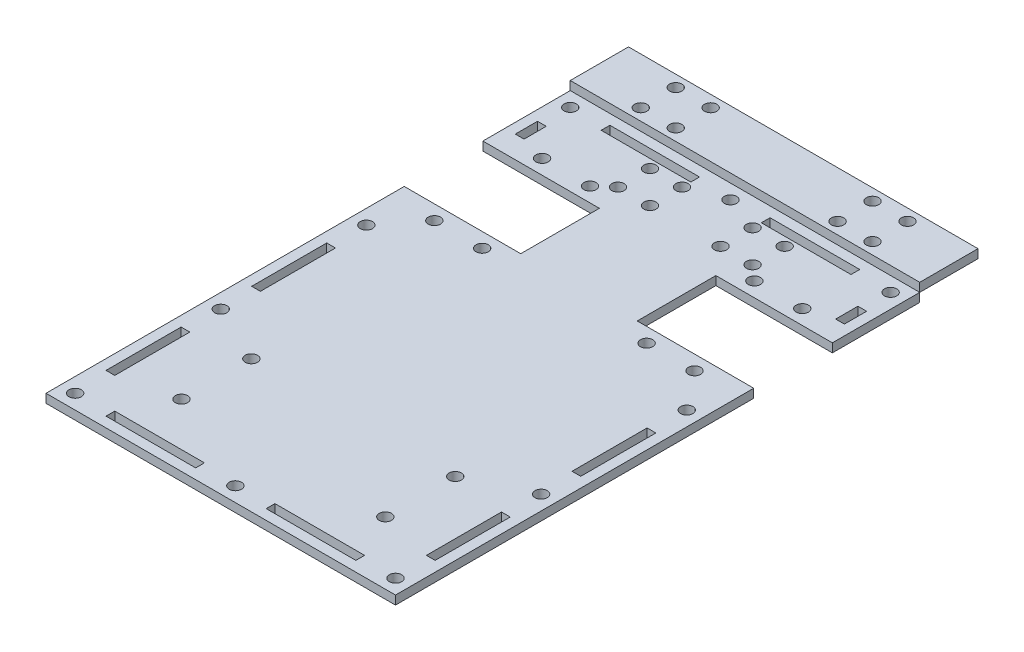
SolidWorks part; units mm, degrees
ref_plane "Front Plane" through (0, 0, 0) normal (0, 0, 1) x (1, 0, 0)
ref_plane "Top Plane" through (0, 0, 0) normal (0, 1, 0) x (1, 0, 0)
ref_plane "Right Plane" through (0, 0, 0) normal (1, 0, 0) x (0, 0, -1)
sketch "Sketch1" plane through (0, 0, 0) normal (0, 1, 0) x (1, 0, 0)
  line L0 (0, 0) -> (120, 0)
  line L1 (0, 0) -> (0, 110)
  line L2 (0, 110) -> (40, 110)
  line L3 (40, 110) -> (40, 150)
  line L4 (40, 150) -> (0, 150)
  line L5 (0, 150) -> (0, 180)
  line L6 (0, 180) -> (120, 180)
  line L7 (120, 180) -> (120, 150)
  line L8 (120, 150) -> (80, 150)
  line L11 (120, 110) -> (120, 0)
  line L12 (80, 150) -> (80, 110)
  line L13 (80, 110) -> (120, 110)
extrude "Boss-Extrude1" add sketch "Sketch1" along normal blind 3 contours L13 L11 L0 L1 L2 L3 L4 L5 L6 L7 L8 L12
sketch "Sketch2" plane through (0, 3, 0) normal (0, 1, 0) x (1, 0, 0)
  line L0 (5, 180) -> (5, 175)
  line L1 (0, 180) -> (120, 180) construction
  line L2 (5, 175) -> (0, 175)
  line L3 (0, 150) -> (0, 180) construction
  line L4 (60, 180) -> (60, 175)
  line L5 (115, 180) -> (115, 175)
  line L6 (115, 175) -> (120, 175)
  line L7 (5, 0) -> (5, 5)
  line L8 (0, 0) -> (120, 0) construction
  line L9 (5, 5) -> (0, 5)
  line L10 (0, 0) -> (0, 110) construction
  line L11 (60, 0) -> (60, 5)
  line L12 (115, 0) -> (115, 5)
  line L13 (115, 5) -> (120, 5)
  line L14 (5, 110) -> (5, 105)
  line L15 (0, 110) -> (40, 110) construction
  line L16 (5, 105) -> (0, 105)
  line L17 (115, 110) -> (115, 105)
  line L18 (115, 105) -> (120, 105)
  line L19 (115, 5) -> (115, 105)
  line L20 (5, 105) -> (5, 5)
  line L21 (115, 5) -> (106.5, 5)
  line L22 (5, 5) -> (13.5, 5)
  line L23 (60, 5) -> (60, 10)
  line L24 (25, 57) -> (25, 45.5)
  line L25 (13.5, 10) -> (106.5, 10)
  line L26 (13.5, 10) -> (13.5, 57)
  line L27 (13.5, 57) -> (106.5, 57)
  line L28 (106.5, 10) -> (106.5, 57)
  line L29 (25, 45.5) -> (13.5, 45.5)
  line L32 (95, 57) -> (95, 45.5)
  line L33 (95, 45.5) -> (106.5, 45.5)
  line L34 (95, 21.5) -> (106.5, 21.5)
  line L35 (95, 10) -> (95, 21.5)
  line L36 (25, 10) -> (25, 21.5)
  line L37 (25, 21.5) -> (13.5, 21.5)
hole_wizard "Hole for M3 300® SC Nuts (SP)1" positions "Sketch3" profile "Sketch4" hole size "M3x0.5" standard "PEM® Metric" end condition through all
sketch "Sketch3" plane through (0, 3, 0) normal (0, 1, 0) x (1, 0, 0)
  point P0 (5, 175)
  point P3 (60, 175)
  point P6 (115, 175)
  point P9 (115, 5)
  point P12 (60, 5)
  point P15 (5, 5)
sketch "Sketch4" plane through (5, 3, -175) normal (1, 0, 0) x (0, 0, 1)
  line L0 (0, 0) -> (0, 3)
  line L1 (0, 3) -> (2.11, 3)
  line L2 (2.11, 3) -> (2.11, 0)
  line L5 (2.11, 0) -> (0, 0)
  line L11 (0, -6.35) -> (0, 107.95) construction
  dimension "Thru Hole Dia." = 4.22
  dimension "Thru Hole Depth" = 3
hole_wizard "Hole for M3 300® SC Nuts (SP)2" positions "Sketch5" profile "Sketch6" hole size "M3x0.5" standard "PEM® Metric" end condition through all
sketch "Sketch5" plane through (0, 3, 0) normal (0, 1, 0) x (1, 0, 0)
  point P0 (5, 105)
  point P3 (115, 105)
sketch "Sketch6" plane through (5, 3, -105) normal (1, 0, 0) x (0, 0, 1)
  line L0 (0, 0) -> (0, 3)
  line L1 (0, 3) -> (2.11, 3)
  line L2 (2.11, 3) -> (2.11, 0)
  line L5 (2.11, 0) -> (0, 0)
  line L11 (0, -6.35) -> (0, 107.95) construction
  dimension "Thru Hole Dia." = 4.22
  dimension "Thru Hole Depth" = 3
hole_wizard "Hole for M3 300® SC Nuts (SP)3" positions "Sketch7" profile "Sketch8" hole size "M3x0.5" standard "PEM® Metric" end condition through all
sketch "Sketch7" plane through (0, 3, 0) normal (0, 1, 0) x (1, 0, 0)
  line L0 (115, 5) -> (115, 105) construction
  line L1 (5, 105) -> (5, 5) construction
  point P0 (115, 55)
  point P4 (5, 55)
sketch "Sketch8" plane through (115, 3, -55) normal (1, 0, 0) x (0, 0, 1)
  line L0 (0, 0) -> (0, 3)
  line L1 (0, 3) -> (2.11, 3)
  line L2 (2.11, 3) -> (2.11, 0)
  line L5 (2.11, 0) -> (0, 0)
  line L11 (0, -6.35) -> (0, 107.95) construction
  dimension "Thru Hole Dia." = 4.22
  dimension "Thru Hole Depth" = 3
sketch "Sketch9" plane through (0, 3, 0) normal (0, 1, 0) x (1, 0, 0)
  line L3 (15.3325, 150) -> (15.3325, 155)
  line L4 (0, 110) -> (40, 110) construction
  line L7 (15.3325, 105) -> (15.3325, 110)
  line L8 (31.7775, 105) -> (31.7775, 110)
  line L9 (40, 150) -> (0, 150) construction
  line L10 (31.7775, 150) -> (31.7775, 155)
  line L11 (60, 180) -> (60, 175)
  line L12 (88.2225, 150) -> (88.2225, 155)
  line L13 (88.2225, 105) -> (88.2225, 110)
  line L14 (104.6675, 105) -> (104.6675, 110)
  line L15 (104.6675, 150) -> (104.6675, 155)
hole_wizard "Hole for M3 300® SC Nuts (SP)4" positions "Sketch10" profile "Sketch11" hole size "M3x0.5" standard "PEM® Metric" end condition through all
sketch "Sketch10" plane through (0, 3, 0) normal (0, 1, 0) x (1, 0, 0)
  point P12 (88.2225, 155)
  point P15 (104.6675, 155)
  point P18 (15.3325, 155)
  point P21 (31.7775, 155)
sketch "Sketch11" plane through (88.2225, 3, -155) normal (1, 0, 0) x (0, 0, 1)
  line L0 (0, 0) -> (0, 3)
  line L1 (0, 3) -> (2.11, 3)
  line L2 (2.11, 3) -> (2.11, 0)
  line L5 (2.11, 0) -> (0, 0)
  line L11 (0, -6.35) -> (0, 107.95) construction
  dimension "Thru Hole Dia." = 4.22
  dimension "Thru Hole Depth" = 3
hole_wizard "Hole for M3 300® SC Nuts (SP)5" positions "Sketch12" profile "Sketch13" hole size "M3x0.5" standard "PEM® Metric" end condition through all
sketch "Sketch12" plane through (0, 3, 0) normal (0, 1, 0) x (1, 0, 0)
  point P0 (25, 45.5)
  point P3 (95, 45.5)
  point P6 (95, 21.5)
  point P9 (25, 21.5)
sketch "Sketch13" plane through (25, 3, -45.5) normal (1, 0, 0) x (0, 0, 1)
  line L0 (0, 0) -> (0, 3)
  line L1 (0, 3) -> (2.11, 3)
  line L2 (2.11, 3) -> (2.11, 0)
  line L5 (2.11, 0) -> (0, 0)
  line L11 (0, -6.35) -> (0, 107.95) construction
  dimension "Thru Hole Dia." = 4.22
  dimension "Thru Hole Depth" = 3
sketch "Sketch15" plane through (0, 3, 0) normal (0, 1, 0) x (1, 0, 0)
  line L0 (60, 180) -> (60, 175)
  line L1 (0, 180) -> (120, 180) construction
  line L2 (72.11, 176.5) -> (102.89, 176.5)
  line L3 (102.89, 173.5) -> (102.89, 176.5)
  line L4 (47.89, 173.5) -> (17.11, 173.5)
  line L5 (47.89, 173.5) -> (47.89, 176.5)
  line L6 (47.89, 176.5) -> (17.11, 176.5)
  line L7 (17.11, 173.5) -> (17.11, 176.5)
  line L8 (72.11, 173.5) -> (102.89, 173.5)
  line L9 (72.11, 173.5) -> (72.11, 176.5)
  line L10 (113.5, 165.26) -> (116.5, 165.26)
  line L11 (116.5, 157.63) -> (116.5, 165.26)
  line L12 (72.11, 6.5) -> (72.11, 3.5)
  line L13 (72.11, 6.5) -> (102.89, 6.5)
  line L14 (102.89, 6.5) -> (102.89, 3.5)
  line L15 (72.11, 3.5) -> (102.89, 3.5)
  line L16 (47.89, 3.5) -> (17.11, 3.5)
  line L17 (17.11, 6.5) -> (17.11, 3.5)
  line L18 (47.89, 6.5) -> (17.11, 6.5)
  line L19 (47.89, 6.5) -> (47.89, 3.5)
  line L20 (6.5, 17.11) -> (6.5, 42.89)
  line L21 (113.5, 157.63) -> (116.5, 157.63)
  line L22 (113.5, 157.63) -> (113.5, 165.26)
  line L23 (6.5, 157.63) -> (3.5, 157.63)
  line L24 (6.5, 157.63) -> (6.5, 165.26)
  line L25 (6.5, 165.26) -> (3.5, 165.26)
  line L26 (3.5, 157.63) -> (3.5, 165.26)
  line L29 (3.5, 42.89) -> (6.5, 42.89)
  line L30 (116.5, 67.11) -> (113.5, 67.11)
  line L31 (3.5, 17.11) -> (6.5, 17.11)
  line L32 (3.5, 17.11) -> (3.5, 42.89)
  line L33 (3.5, 92.89) -> (6.5, 92.89)
  line L34 (3.5, 92.89) -> (3.5, 67.11)
  line L35 (3.5, 67.11) -> (6.5, 67.11)
  line L36 (6.5, 92.89) -> (6.5, 67.11)
  line L38 (113.5, 92.89) -> (113.5, 67.11)
  line L39 (116.5, 92.89) -> (113.5, 92.89)
  line L40 (116.5, 92.89) -> (116.5, 67.11)
  line L41 (116.5, 17.11) -> (113.5, 17.11)
  line L42 (116.5, 17.11) -> (116.5, 42.89)
  line L43 (116.5, 42.89) -> (113.5, 42.89)
  line L44 (113.5, 17.11) -> (113.5, 42.89)
extrude "Cut-Extrude1" cut sketch "Sketch15" against normal through all contours L9 L8 L3 L2 | L7 L4 L5 L6 | L26 L23 L24 L25 | L22 L21 L11 L10 | L36 L33 L34 L35 | L40 L39 L38 L30 | L44 L41 L42 L43 | L32 L31 L20 L29 | L19 L18 L17 L16 | L12 L15 L14 L13
sketch "Sketch16" plane through (0, 3, 0) normal (0, 1, 0) x (1, 0, 0)
  line L1 (0, 180) -> (120, 180)
  line L2 (0, 180) -> (0, 200)
  line L3 (0, 200) -> (120, 200)
  line L4 (120, 180) -> (120, 200)
  line L6 (0, 0) -> (120, 0) construction
extrude "Boss-Extrude3" add sketch "Sketch16" along normal blind 3 separate body contours L2 L1 L4 L3
sketch "Sketch17" plane through (0, 6, 0) normal (0, 1, 0) x (1, 0, 0)
  line L2 (26.21, 184) -> (32.21, 184)
  line L4 (99.79, 196) -> (99.79, 184)
  line L6 (32.21, 184) -> (32.21, 196)
  line L8 (32.21, 196) -> (20.21, 196)
  line L13 (20.21, 196) -> (20.21, 184)
  line L14 (20.21, 184) -> (26.21, 184)
  line L15 (87.79, 196) -> (99.79, 196)
  line L16 (87.79, 184) -> (87.79, 196)
  line L17 (93.79, 184) -> (87.79, 184)
  line L18 (99.79, 184) -> (93.79, 184)
hole_wizard "Hole for M3 300® SC Nuts (SP)6" positions "Sketch18" profile "Sketch19" hole size "M3x0.5" standard "PEM® Metric" end condition through all
sketch "Sketch18" plane through (0, 6, 0) normal (0, 1, 0) x (1, 0, 0)
  point P0 (20.21, 196)
  point P3 (32.21, 196)
  point P6 (20.21, 184)
  point P9 (32.21, 184)
  point P12 (99.79, 196)
  point P15 (87.79, 196)
  point P18 (87.79, 184)
  point P21 (99.79, 184)
sketch "Sketch19" plane through (20.21, 6, -196) normal (1, 0, 0) x (0, 0, 1)
  line L0 (0, 0) -> (0, 6)
  line L1 (0, 6) -> (2.11, 6)
  line L2 (2.11, 6) -> (2.11, 0)
  line L5 (2.11, 0) -> (0, 0)
  line L11 (0, -6.35) -> (0, 107.95) construction
  dimension "Thru Hole Dia." = 4.22
  dimension "Thru Hole Depth" = 6
sketch "Sketch26" plane through (0, 3, 0) normal (0, 1, 0) x (1, 0, 0)
  line L5 (47.89, 170.5) -> (36.89, 170.5)
  line L6 (47.89, 170.5) -> (47.89, 159.5)
  line L7 (47.89, 159.5) -> (36.89, 159.5)
  line L8 (36.89, 170.5) -> (36.89, 159.5)
  line L9 (72.11, 159.5) -> (83.11, 159.5)
  line L10 (83.11, 170.5) -> (83.11, 159.5)
  line L11 (72.11, 170.5) -> (83.11, 170.5)
  line L12 (72.11, 170.5) -> (72.11, 159.5)
hole_wizard "Hole for M3 300® SC Nuts (SP)8" positions "Sketch29" profile "Sketch30" hole size "M3x0.5" standard "PEM® Metric" end condition through all
sketch "Sketch29" plane through (0, 3, 0) normal (0, 1, 0) x (1, 0, 0)
  point P0 (36.89, 159.5)
  point P3 (36.89, 170.5)
  point P6 (47.89, 170.5)
  point P9 (47.89, 159.5)
  point P12 (72.11, 159.5)
  point P15 (83.11, 159.5)
  point P18 (83.11, 170.5)
  point P21 (72.11, 170.5)
sketch "Sketch30" plane through (36.89, 3, -159.5) normal (1, 0, 0) x (0, 0, 1)
  line L0 (0, 0) -> (0, 3)
  line L1 (0, 3) -> (2.11, 3)
  line L2 (2.11, 3) -> (2.11, 0)
  line L5 (2.11, 0) -> (0, 0)
  line L11 (0, -6.35) -> (0, 107.95) construction
  dimension "Thru Hole Dia." = 4.22
  dimension "Thru Hole Depth" = 3
sketch "Sketch31" plane through (0, 3, 0) normal (0, 1, 0) x (1, 0, 0)
  line L0 (0, 110) -> (0, 123)
  line L1 (0, 123) -> (40, 123)
  line L2 (40, 110) -> (40, 150) construction
  line L3 (120, 110) -> (120, 123)
  line L4 (120, 123) -> (80, 123)
  line L5 (80, 150) -> (80, 110) construction
  line L6 (80, 123) -> (80, 110)
  line L7 (80, 110) -> (120, 110)
  line L8 (40, 123) -> (40, 110)
  line L9 (40, 110) -> (0, 110)
extrude "Boss-Extrude4" add sketch "Sketch31" against normal blind 3 separate body contours L9 L8 L1 L0 | L7 L3 L4 L6
sketch "Sketch32" plane through (0, 3, 0) normal (0, 1, 0) x (1, 0, 0)
  line L0 (40, 118) -> (0, 118)
  line L1 (120, 123) -> (80, 123) construction
  line L2 (88.2225, 123) -> (88.2225, 110)
  line L3 (88.2225, 110) -> (104.6675, 110)
  line L4 (104.6675, 110) -> (104.6675, 123)
  line L5 (80, 150) -> (80, 110) construction
  line L6 (80, 118) -> (120, 118)
  line L7 (120, 110) -> (120, 123) construction
  line L8 (40, 110) -> (40, 150) construction
  line L9 (0, 110) -> (0, 123) construction
  line L11 (15.3325, 110) -> (15.3325, 123)
  line L12 (0, 123) -> (40, 123) construction
  line L13 (31.7775, 110) -> (31.7775, 123)
hole_wizard "Hole for M3 300® SC Nuts (SP)9" positions "Sketch33" profile "Sketch34" hole size "M3x0.5" standard "PEM® Metric" end condition through all
sketch "Sketch33" plane through (0, 3, 0) normal (0, 1, 0) x (1, 0, 0)
  line L0 (40, 118) -> (0, 118) construction
  line L1 (15.3325, 110) -> (15.3325, 123) construction
  line L2 (31.7775, 110) -> (31.7775, 123) construction
  line L3 (88.2225, 123) -> (88.2225, 110) construction
  line L4 (80, 118) -> (120, 118) construction
  line L5 (104.6675, 110) -> (104.6675, 123) construction
  point P0 (15.3325, 118)
  point P6 (31.7775, 118)
  point P10 (88.2225, 118)
  point P16 (104.6675, 118)
sketch "Sketch34" plane through (15.3325, 3, -118) normal (1, 0, 0) x (0, 0, 1)
  line L0 (0, 0) -> (0, 3)
  line L1 (0, 3) -> (2.11, 3)
  line L2 (2.11, 3) -> (2.11, 0)
  line L5 (2.11, 0) -> (0, 0)
  line L11 (0, -6.35) -> (0, 107.95) construction
  dimension "Thru Hole Dia." = 4.22
  dimension "Thru Hole Depth" = 3
sketch "Sketch35" plane through (0, 3, 0) normal (0, 1, 0) x (1, 0, 0)
  line L1 (37.229, 108.4497) -> (41.3114, 108.4497)
  line L2 (37.229, 108.4497) -> (37.229, 123)
  line L3 (37.229, 123) -> (41.3114, 123)
  line L4 (41.3114, 108.4497) -> (41.3114, 123)
  line L6 (82.8017, 123) -> (78.4682, 123)
  line L7 (82.8017, 123) -> (82.8017, 108.4497)
  line L8 (82.8017, 108.4497) -> (78.4682, 108.4497)
  line L9 (78.4682, 123) -> (78.4682, 108.4497)
  line L10 (120, 123) -> (80, 123) construction
extrude "Boss-Extrude5" add sketch "Sketch35" against normal blind 3
